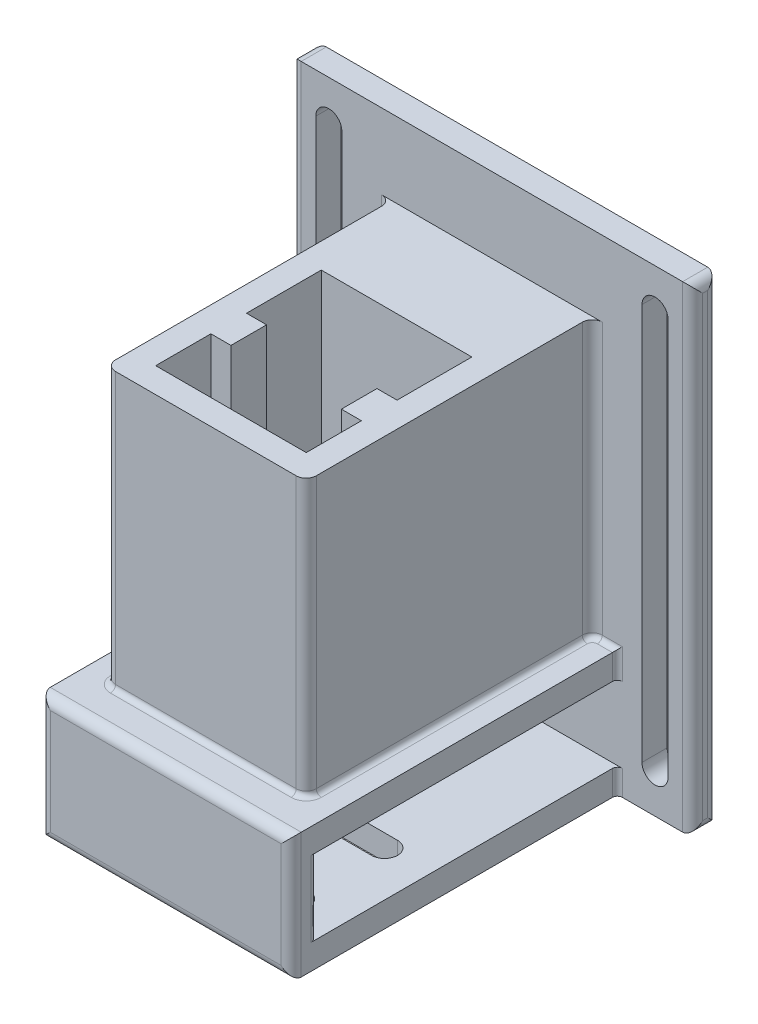
SolidWorks part; units mm, degrees
ref_plane "前视基准面" through (0, 0, 0) normal (0, 0, 1) x (1, 0, 0)
ref_plane "上视基准面" through (0, 0, 0) normal (0, 1, 0) x (1, 0, 0)
ref_plane "右视基准面" through (0, 0, 0) normal (1, 0, 0) x (0, 0, -1)
sketch "草图1" plane through (0, 0, 0) normal (0, 1, 0) x (1, 0, 0)
  line L5 (-20, 40) -> (20, 40)
  line L6 (-20, 40) -> (-20, -20)
  line L7 (-20, -20) -> (20, -20)
  line L8 (20, 40) -> (20, -20)
  dimension "D1" = 40
  dimension "D2" = 40
  dimension "D3" = 20
  dimension "D4" = 20
extrude "凸台-拉伸1" add sketch "草图1" along normal blind 55
sketch "草图2" plane through (0, 55, 0) normal (0, 1, 0) x (1, 0, 0)
  line L0 (0, 27.9716) -> (0, -27.9716) construction
  line L2 (-15, 15) -> (-15, 3.1)
  line L3 (-15, -15) -> (15, -15)
  line L4 (15, 15) -> (15, 3.1)
  line L5 (-15, 15) -> (15, -15) construction
  line L6 (-15, -15) -> (15, 15) construction
  line L7 (15, -4) -> (11, -4)
  line L9 (15, 3.1) -> (11, 3.1)
  line L10 (11, -4) -> (11, 3.1)
  line L11 (-15, -4) -> (-11, -4)
  line L12 (-11, -4) -> (-11, 3.1)
  line L13 (-15, 3.1) -> (-11, 3.1)
  line L14 (-15, -4) -> (-15, -15)
  line L15 (15, -4) -> (15, -15)
  line L16 (-20, -20) -> (20, -20) construction
  line L19 (15, 15) -> (15, 18)
  line L20 (15, 18) -> (-15, 18)
  line L21 (-15, 15) -> (-15, 18)
  point P0 (0, 0)
  point P13 (0, 0)
  dimension "D1" = 30
  dimension "D2" = 11
  dimension "D3" = 4
  dimension "D4" = 7.1
  dimension "D6" = 5
  dimension "D7" = 3
extrude "切除-拉伸1" cut sketch "草图2" against normal blind 50
ref_plane "基准面2" through (0, 0, 0) normal (0, -1, 0) x (-1, 0, 0)
sketch "草图6" plane through (0, 0, 0) normal (0, -1, 0) x (-1, 0, 0)
  line L0 (20, -20) -> (-20, -20) construction
  line L1 (-25, -28) -> (25, -28)
  line L2 (-25, -28) -> (-25, 42)
  line L3 (-25, 42) -> (25, 42)
  line L4 (25, -28) -> (25, 42)
  dimension "D1" = 8
  dimension "D2" = 70
  dimension "D3" = 25
  dimension "D4" = 50
extrude "凸台-拉伸2" add sketch "草图6" along normal blind 25
sketch "草图7" plane through (25, 0, 0) normal (1, 0, 0) x (0, 0, -1)
  line L0 (-28, -25) -> (-28, 0) construction
  line L1 (-23, -5) -> (37, -5)
  line L2 (-23, -5) -> (-23, -20)
  line L3 (-23, -20) -> (37, -20)
  line L4 (37, -5) -> (37, -20)
  line L5 (-56.5748, 0) -> (56.5748, 0) construction
  line L6 (42, -25) -> (42, 0) construction
  line L7 (42, -25) -> (-28, -25) construction
  dimension "D1" = 5
  dimension "D2" = 5
  dimension "D3" = 5
  dimension "D4" = 5
extrude "切除-拉伸2" cut sketch "草图7" against normal through all
sketch "草图8" plane through (0, -25, 0) normal (0, -1, 0) x (1, 0, 0)
  line L0 (-16, 18) -> (16, 18) construction
  line L1 (-16, 20.6) -> (16, 20.6)
  line L2 (-16, 15.4) -> (16, 15.4)
  line L3 (-16, 0.4) -> (16, 0.4) construction
  line L4 (-16, 3) -> (16, 3)
  line L5 (-16, -2.2) -> (16, -2.2)
  line L6 (0, 0) -> (0, 40.8428) construction
  line L7 (0, 0) -> (0, -53.3315) construction
  line L8 (25, 28) -> (-25, 28) construction
  arc A0 (-16, 20.6) -> (-16, 15.4) centre (-16, 18) ccw
  arc A1 (16, 15.4) -> (16, 20.6) centre (16, 18) ccw
  arc A2 (-16, 3) -> (-16, -2.2) centre (-16, 0.4) ccw
  arc A3 (16, -2.2) -> (16, 3) centre (16, 0.4) ccw
  point P2 (0, 18)
  point P9 (0, 0.4)
  dimension "D1" = 2.6
  dimension "D2" = 2.6
  dimension "D3" = 32
  dimension "D4" = 32
  dimension "D5" = 10
  dimension "D6" = 15
  dimension "D7" = 17.6
extrude "切除-拉伸3" cut sketch "草图8" against normal up to next
sketch "草图10" plane through (0, 0, 0) normal (0, 1, 0) x (1, 0, 0)
  line L5 (-25, 42) -> (25, 42) construction
  line L6 (-40, 42) -> (40, 42)
  line L7 (-40, 42) -> (-40, 37)
  line L8 (-40, 37) -> (40, 37)
  line L9 (40, 42) -> (40, 37)
  line L10 (-25, -28) -> (-25, 42) construction
  line L11 (25, 42) -> (25, -28) construction
  dimension "D1" = 5
  dimension "D2" = 15
  dimension "D3" = 15
extrude "凸台-拉伸3" add sketch "草图10" along normal blind 70 and the other way blind 25
sketch "草图11" plane through (0, 0, -42) normal (0, 0, -1) x (-1, 0, 0)
  line L0 (0, 0) -> (0, 70) construction
  line L1 (-40, 70) -> (40, 70) construction
  line L2 (-32.5, 70) -> (-32.5, -25) construction
  line L3 (-40, -25) -> (40, -25) construction
  line L4 (-40, 70) -> (-40, -25) construction
  line L5 (-32.5, 62) -> (-32.5, -17) construction
  line L6 (-29.9, 62) -> (-29.9, -17)
  line L7 (-35.1, 62) -> (-35.1, -17)
  line L8 (32.5, 62) -> (32.5, -17) construction
  line L9 (29.9, 62) -> (29.9, -17)
  line L10 (35.1, 62) -> (35.1, -17)
  arc A0 (-29.9, 62) -> (-35.1, 62) centre (-32.5, 62) ccw
  arc A1 (-35.1, -17) -> (-29.9, -17) centre (-32.5, -17) ccw
  arc A2 (29.9, 62) -> (35.1, 62) centre (32.5, 62) cw
  arc A3 (35.1, -17) -> (29.9, -17) centre (32.5, -17) cw
  point P13 (-32.5, 22.5)
  point P21 (32.5, 22.5)
  dimension "D2" = 2.6
  dimension "D1" = 7.5
  dimension "D3" = 8
  dimension "D4" = 8
extrude "切除-拉伸4" cut sketch "草图11" against normal up to next
fillet "圆角1" radius 2 16 edges at (25, -12.5, 28) (0, -25, 28) (-25, -12.5, 28) (0, 0, 28) (40, 70, -39.5) (40, -25, -39.5) (40, 22.5, -37) (40, 22.5, -42) (-40, 70, -39.5) (-40, -25, -39.5) (-40, 22.5, -42) (-40, 22.5, -37) (20, 27.5, -37) (20, 27.5, 20) (-20, 27.5, 20) (-20, 27.5, -37)
fillet "圆角2" radius 1 9 edges at (-23.5, 0, -37) (-20.5858, 0, -36.4142) (23.5, 0, -37) (20.5858, 0, -36.4142) (20, 0, -8.5) (19.4142, 0, 19.4142) (0, 0, 20) (-19.4142, 0, 19.4142) (-20, 0, -8.5)
fillet "圆角3" radius 1 6 edges at (25, -12.5, 23) (-25, -12.5, 23) (-25, -22.5, -37) (-25, -2, -37) (25, -22.5, -37) (25, -2, -37)
